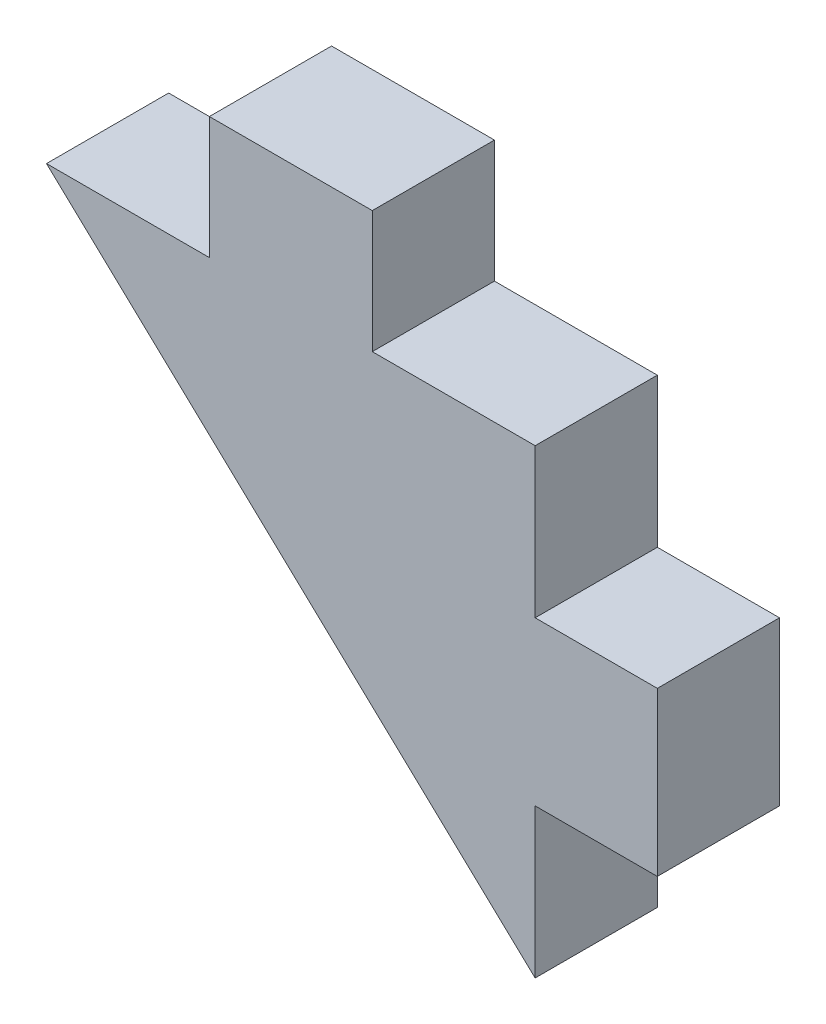
SolidWorks part; units mm, degrees
ref_plane "Front Plane" through (0, 0, 0) normal (0, 0, 1) x (1, 0, 0)
ref_plane "Top Plane" through (0, 0, 0) normal (0, 1, 0) x (1, 0, 0)
ref_plane "Right Plane" through (0, 0, 0) normal (1, 0, 0) x (0, 0, -1)
sketch "Sketch1" plane through (0, 0, 0) normal (0, 0, 1) x (1, 0, 0)
  line L0 (-10, 9.434) -> (10, -9.434)
  line L1 (3.3333, 9.434) -> (10, 9.434)
  line L2 (10, 3.3333) -> (10, 9.434)
  line L3 (-10, 9.434) -> (-3.3333, 9.434)
  line L4 (10, -9.434) -> (10, -3.3333)
  line L5 (0, 0) -> (10, 9.434) construction
  line L6 (-10, 9.434) -> (10, -9.434) construction
  line L8 (-3.3333, 9.434) -> (-3.3333, 14.434)
  line L9 (-3.3333, 14.434) -> (3.3333, 14.434)
  line L10 (3.3333, 9.434) -> (3.3333, 14.434)
  line L11 (0, 10.3346) -> (3.3333, 14.434) construction
  line L12 (-3.3333, 14.434) -> (0, 10.3346) construction
  line L13 (10, -3.3333) -> (15, -3.3333)
  line L15 (10, 3.3333) -> (15, 3.3333)
  line L16 (15, -3.3333) -> (15, 3.3333)
  line L17 (10, 0) -> (15, 3.3333) construction
  line L18 (10, 0) -> (15, -3.3333) construction
  point P0 (0, 0)
  point P6 (0, 10.3346)
  point P11 (10, 0)
  dimension "D1" = 5
  dimension "D2" = 6.6667
  dimension "D3" = 6.6667
  dimension "D4" = 5
extrude "Boss-Extrude1" add sketch "Sketch1" along normal blind 5
equation "\"D1@Boss-Extrude1\" = \"mat@v1.assembly\""
equation "\"D4@Sketch1\" = \"mat@V1.assembly\""
equation "\"D1@Sketch1\"=\"mat@V1.assembly\""
